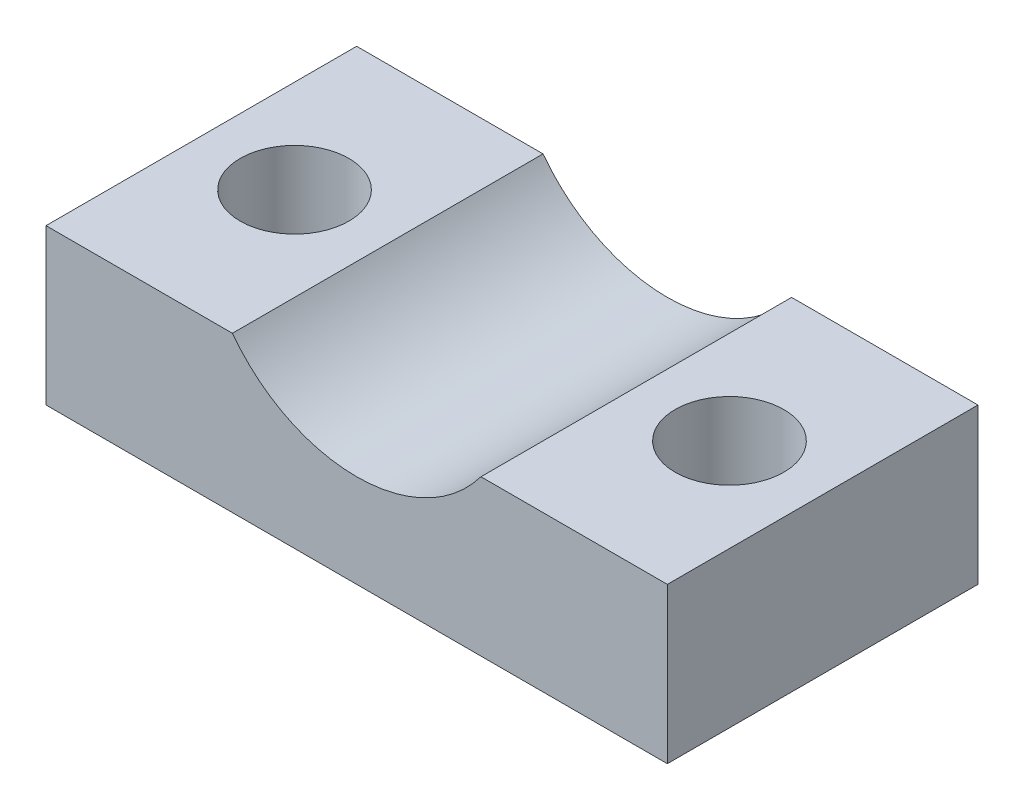
SolidWorks part; units mm, degrees
ref_plane "Ebene vorne" through (0, 0, 0) normal (0, 0, 1) x (1, 0, 0)
ref_plane "Ebene oben" through (0, 0, 0) normal (0, 1, 0) x (1, 0, 0)
ref_plane "Ebene rechts" through (0, 0, 0) normal (1, 0, 0) x (0, 0, -1)
sketch "Skizze1" plane through (0, 0, 0) normal (0, 0, 1) x (1, 0, 0)
  line L0 (0, 0) -> (20, 0)
  line L1 (20, 0) -> (20, 5)
  line L2 (20, 5) -> (14, 5)
  line L3 (0, 0) -> (0, 5)
  line L4 (0, 5) -> (6, 5)
  arc A0 (6, 5) -> (14, 5) centre (10, 8) ccw
  point P7 (10, 3)
  dimension "D1" = 6
  dimension "D2" = 6
  dimension "D3" = 2
  dimension "D4" = 5
  dimension "D5" = 20
  dimension "D6" = 0
  dimension "D7" = 0
  dimension "D8" = 0
extrude "Aufsatz-Linear austragen1" add sketch "Skizze1" along normal blind 10
sketch "Skizze2" plane through (0, 5, 0) normal (0, 1, 0) x (1, 0, 0)
  line L0 (6, 0) -> (0, 0) construction
  line L1 (0, -10) -> (0, 0) construction
  line L2 (20, -10) -> (20, 0) construction
  circle A0 centre (3, -5) radius 1.75
  circle A1 centre (17, -5) radius 1.75
  dimension "D5" = 3.5
  dimension "D6" = 3.5
  dimension "D1" = 5
  dimension "D2" = 0
  dimension "D3" = 3
  dimension "D4" = 3
extrude "Schnitt-Linear austragen1" cut sketch "Skizze2" against normal through all
